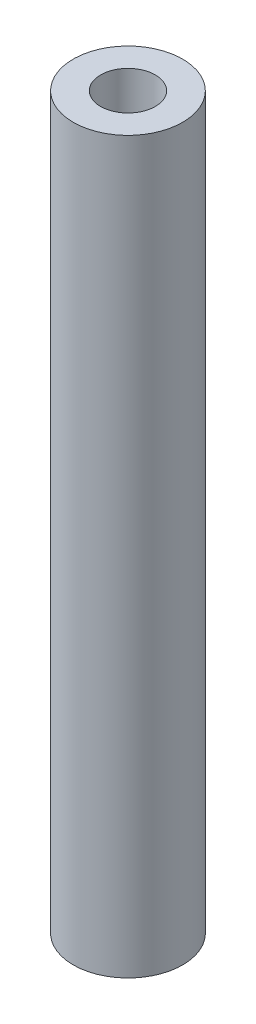
SolidWorks part; units mm, degrees
ref_plane "Front Plane" through (0, 0, 0) normal (0, 0, 1) x (1, 0, 0)
ref_plane "Top Plane" through (0, 0, 0) normal (0, 1, 0) x (1, 0, 0)
ref_plane "Right Plane" through (0, 0, 0) normal (1, 0, 0) x (0, 0, -1)
sketch "Sketch1" plane through (0, 0, 0) normal (0, 1, 0) x (1, 0, 0)
  circle A0 centre (0, 0) radius 6
  circle A1 centre (0, 0) radius 1.5
  dimension "D1" = 3
  dimension "D2" = 12
extrude "Boss-Extrude1" add sketch "Sketch1" along normal blind 80
sketch "Sketch2" plane through (0, 80, 0) normal (0, 1, 0) x (1, 0, 0)
  circle A0 centre (0, 0) radius 3
  dimension "D1" = 6
extrude "Cut-Extrude1" cut sketch "Sketch2" against normal blind 5
